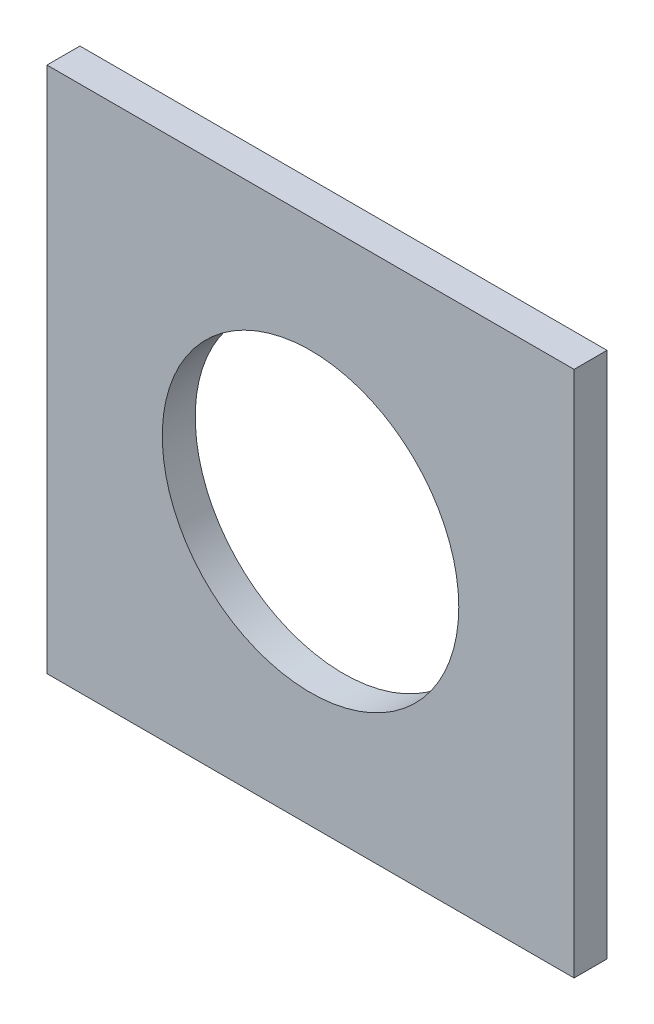
SolidWorks part; units mm, degrees
ref_plane "Front Plane" through (0, 0, 0) normal (0, 0, 1) x (1, 0, 0)
ref_plane "Top Plane" through (0, 0, 0) normal (0, 1, 0) x (1, 0, 0)
ref_plane "Right Plane" through (0, 0, 0) normal (1, 0, 0) x (0, 0, -1)
sketch "Sketch1" plane through (0, 0, 0) normal (0, 0, 1) x (1, 0, 0)
  line L1 (-20.4569, 17.1108) -> (30.3431, 17.1108)
  line L2 (-20.4569, 17.1108) -> (-20.4569, -33.6892)
  line L3 (-20.4569, -33.6892) -> (30.3431, -33.6892)
  line L4 (30.3431, 17.1108) -> (30.3431, -33.6892)
  dimension "D1" = 50.8
  dimension "D2" = 50.8
extrude "Boss-Extrude1" add sketch "Sketch1" along normal blind 3.175
sketch "Sketch2" plane through (0, 0, 3.175) normal (0, 0, 1) x (1, 0, 0)
  line L0 (4.9431, 17.1108) -> (4.9431, -33.6892)
  line L1 (30.3431, 17.1108) -> (-20.4569, 17.1108) construction
  line L2 (-20.4569, -33.6892) -> (30.3431, -33.6892) construction
  line L3 (-20.4569, -8.2892) -> (30.3431, -8.2892)
  line L4 (-20.4569, 17.1108) -> (-20.4569, -33.6892) construction
  line L5 (30.3431, -33.6892) -> (30.3431, 17.1108) construction
  circle A0 centre (4.9431, -8.2892) radius 14.2875
  dimension "D1" = 28.575
extrude "Cut-Extrude1" cut sketch "Sketch2" against normal blind 3.175 contours L0 A0 L3 | L3 A0 L0 | L0 A0 L3 | L3 A0 L0
